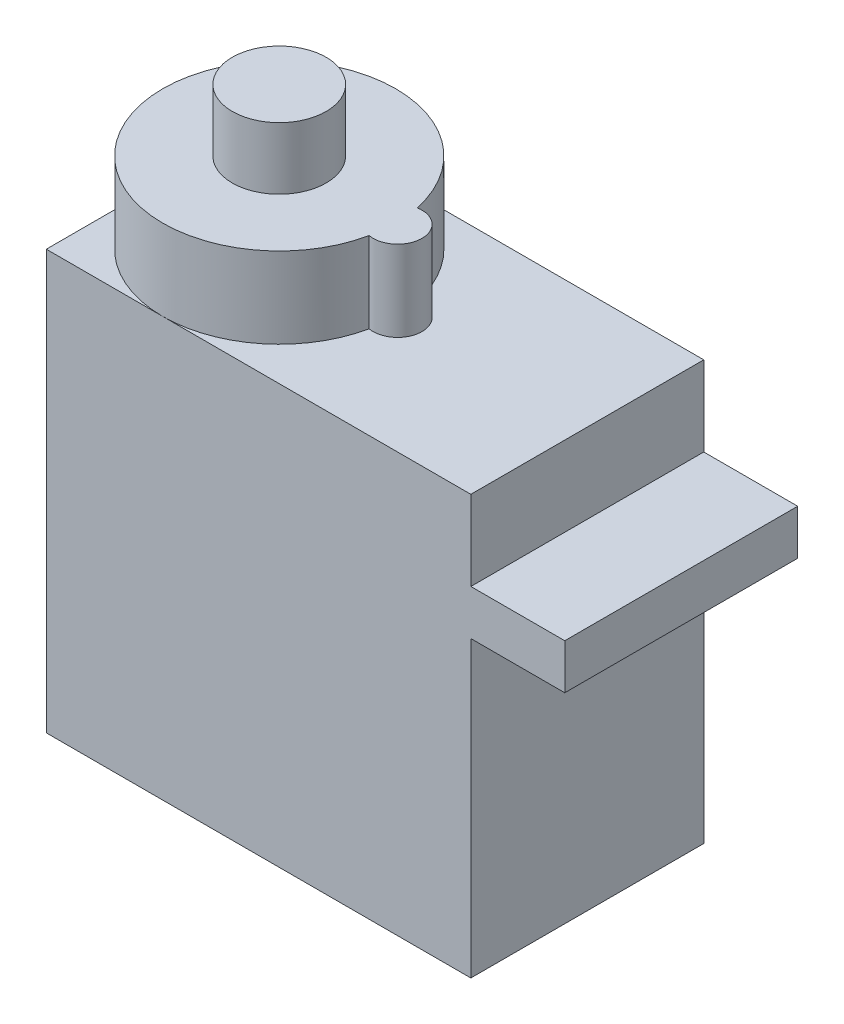
SolidWorks part; units mm, degrees
ref_plane "Front Plane" through (0, 0, 0) normal (0, 0, 1) x (1, 0, 0)
ref_plane "Top Plane" through (0, 0, 0) normal (0, 1, 0) x (1, 0, 0)
ref_plane "Right Plane" through (0, 0, 0) normal (1, 0, 0) x (0, 0, -1)
sketch "Sketch1" plane through (0, 0, 0) normal (0, 1, 0) x (1, 0, 0)
  line L1 (-11.3, -6.2) -> (11.3, -6.2)
  line L2 (-11.3, -6.2) -> (-11.3, 6.2)
  line L3 (-11.3, 6.2) -> (11.3, 6.2)
  line L4 (11.3, -6.2) -> (11.3, 6.2)
  line L5 (-11.3, -6.2) -> (11.3, 6.2) construction
  line L6 (-11.3, 6.2) -> (11.3, -6.2) construction
  point P0 (0, 0)
  dimension "D1" = 22.6
  dimension "D2" = 12.4
extrude "Boss-Extrude1" add sketch "Sketch1" along normal blind 22.3
sketch "Sketch2" plane through (11.3, 0, 0) normal (1, 0, 0) x (0, 0, -1)
  line L0 (-6.2, 22.3) -> (-6.2, 0) construction
  line L1 (-6.2, 18.05) -> (6.2, 18.05)
  line L2 (-6.2, 18.05) -> (-6.2, 15.65)
  line L3 (-6.2, 15.65) -> (6.2, 15.65)
  line L4 (6.2, 18.05) -> (6.2, 15.65)
  line L5 (6.2, 22.3) -> (6.2, 0) construction
  line L6 (-6.2, 22.3) -> (6.2, 22.3) construction
  dimension "D1" = 4.25
  dimension "D2" = 2.4
extrude "Boss-Extrude2" add sketch "Sketch2" along normal blind 5
sketch "Sketch5" plane through (0, 18.05, 0) normal (0, 1, 0) x (1, 0, 0)
  line L0 (16.3, 6.2) -> (16.3, -6.2) construction
  line L1 (14.6352, 0.55) -> (16.3, 0.55)
  line L3 (14.6352, -0.55) -> (16.3, -0.55)
  line L4 (16.3, 0.55) -> (16.3, -0.55)
  arc A0 (14.6352, 0.55) -> (14.6352, -0.55) centre (13.8, 0) ccw
  dimension "D1" = 2
  dimension "D2" = 1.1
  dimension "D3" = 0.55
  dimension "D4" = 2.5
extrude "Cut-Extrude2" [suppressed] cut sketch "Sketch5" against normal up to next contours L1 L4 L3 A0
sketch "Sketch6" plane through (0, 22.3, 0) normal (0, 1, 0) x (1, 0, 0)
  line L0 (-11.3, 6.2) -> (-11.3, -6.2) construction
  line L1 (1.2, 1.3) -> (0.9622, 1.3)
  line L2 (1.2, -1.3) -> (0.9622, -1.3)
  arc A0 (0.9667, 1.2789) -> (0.9667, -1.2789) centre (-5.1, 0) ccw
  arc A1 (0.9667, -1.2789) -> (0.9667, 1.2789) centre (1.2, 0) ccw
  dimension "D2" = 12.4
  dimension "D3" = 2.6
  dimension "D1" = 6.2
  dimension "D4" = 6.3
extrude "Boss-Extrude4" add sketch "Sketch6" along normal blind 4.3 contours A1 A0
sketch "Sketch7" plane through (0, 26.6, 0) normal (0, 1, 0) x (1, 0, 0)
  circle A0 centre (-5.1, 0) radius 2.5
  dimension "D1" = 5
extrude "Boss-Extrude5" add sketch "Sketch7" along normal blind 3.3
inserted part "Microservo horn" [suppressed]
move or copy body "Body-Move/Copy1" [suppressed] bodies to move or copy 111 placed by mates yes
combine bodies "Combine1" [suppressed] operation type add bodies to combine 107 112
